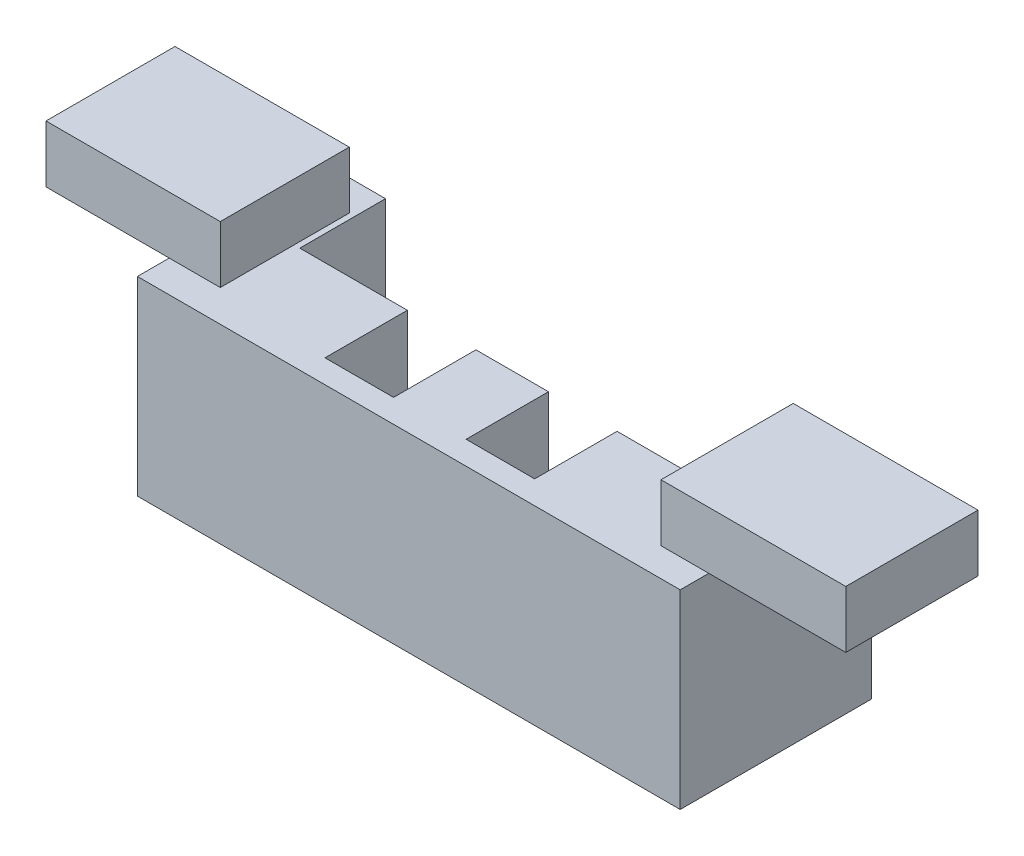
SolidWorks part; units mm, degrees
ref_plane "Front Plane" through (0, 0, 0) normal (0, 0, 1) x (1, 0, 0)
ref_plane "Top Plane" through (0, 0, 0) normal (0, 1, 0) x (1, 0, 0)
ref_plane "Right Plane" through (0, 0, 0) normal (1, 0, 0) x (0, 0, -1)
sketch "Sketch1" plane through (0, 0, 0) normal (0, 1, 0) x (1, 0, 0)
  line L1 (0, 0) -> (48.26, 0)
  line L2 (0, 0) -> (0, 17.018)
  line L3 (0, 17.018) -> (48.26, 17.018)
  line L4 (48.26, 0) -> (48.26, 17.018)
  dimension "D1" = 48.26
  dimension "D2" = 17.018
extrude "Boss-Extrude1" add sketch "Sketch1" along normal blind 16.9164
sketch "Sketch3" plane through (0, 0, -17.018) normal (0, 0, -1) x (-1, 0, 0)
  line L0 (-48.26, 16.9164) -> (0, 16.9164) construction
  line L1 (-43.5441, 16.9164) -> (-5.0406, 16.9164)
  line L2 (-43.5441, 16.9164) -> (-43.5441, 1.6865)
  line L3 (-43.5441, 1.6865) -> (-5.0406, 1.6865)
  line L4 (-5.0406, 16.9164) -> (-5.0406, 1.6865)
extrude "Cut-Extrude1" cut sketch "Sketch3" against normal blind 7.62
sketch "Sketch4" plane through (0, 1.6865, 0) normal (0, 1, 0) x (1, 0, 0)
  line L0 (43.5441, 17.018) -> (5.0406, 17.018) construction
  line L1 (14.6033, 17.018) -> (20.6993, 17.018)
  line L2 (14.6033, 17.018) -> (14.6033, 2.074)
  line L3 (14.6033, 2.074) -> (20.6993, 2.074)
  line L4 (20.6993, 17.018) -> (20.6993, 2.074)
  line L6 (27.1498, 2.074) -> (33.2458, 2.074)
  line L7 (27.1498, 2.074) -> (27.1498, 17.018)
  line L8 (27.1498, 17.018) -> (33.2458, 17.018)
  line L9 (33.2458, 2.074) -> (33.2458, 17.018)
  dimension "D1" = 6.096
  dimension "D2" = 6.096
extrude "Cut-Extrude2" cut sketch "Sketch4" along normal blind 15.24
sketch "Sketch5" plane through (0, 16.9164, 0) normal (0, 1, 0) x (1, 0, 0)
  line L1 (-10.9571, 14.2969) -> (4.5373, 14.2969)
  line L2 (-10.9571, 14.2969) -> (-10.9571, 2.8289)
  line L3 (-10.9571, 2.8289) -> (4.5373, 2.8289)
  line L4 (4.5373, 14.2969) -> (4.5373, 2.8289)
  line L5 (44.0103, 14.2969) -> (60.4394, 14.2969)
  line L6 (44.0103, 14.2969) -> (44.0103, 2.5413)
  line L7 (44.0103, 2.5413) -> (60.4394, 2.5413)
  line L8 (60.4394, 14.2969) -> (60.4394, 2.5413)
  point P8 (45.5562, 14.2969)
  point P9 (-10.9571, 2.6492)
  point P10 (4.5373, 2.8289)
  point P11 (44.0103, 2.5413)
extrude "Boss-Extrude2" add sketch "Sketch5" along normal blind 5.08
